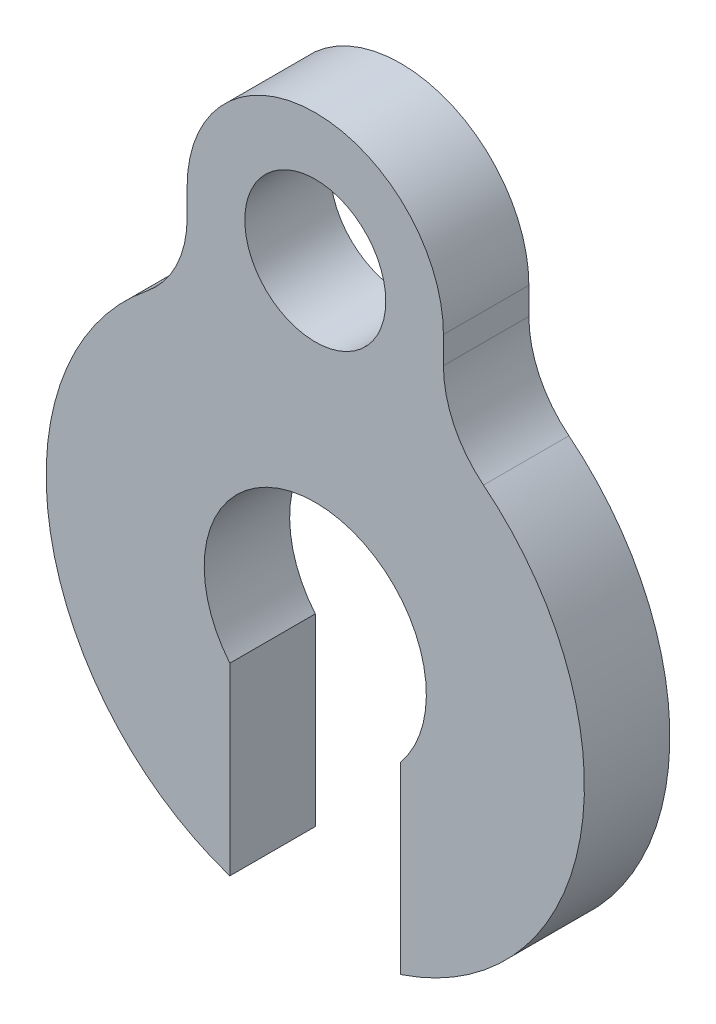
SolidWorks part; units mm, degrees
ref_plane "Front Plane" through (0, 0, 0) normal (0, 0, 1) x (1, 0, 0)
ref_plane "Top Plane" through (0, 0, 0) normal (0, 1, 0) x (1, 0, 0)
ref_plane "Right Plane" through (0, 0, 0) normal (1, 0, 0) x (0, 0, -1)
sketch "Sketch1" plane through (0, 0, 0) normal (0, 0, 1) x (1, 0, 0)
  line L0 (0, -57.8923) -> (0, 2836.7216) construction
  line L1 (-1.905, 3.5178) -> (-1.905, 4.7625)
  line L2 (1.905, 4.7625) -> (1.905, 3.5178)
  line L3 (-1.27, -3.7936) -> (-1.27, -1.0549)
  line L4 (1.27, -3.7936) -> (1.27, -1.0549)
  circle A0 centre (0, 0) radius 1.651 construction
  circle A1 centre (0, 4.7625) radius 1.0478
  arc A2 (-1.905, 4.7625) -> (1.905, 4.7625) centre (0, 4.7625) cw
  arc A3 (-1.905, 3.5178) -> (-1.27, -3.7936) centre (0, 0) ccw
  arc A4 (1.905, 3.5178) -> (1.27, -3.7936) centre (0, 0) cw
  arc A5 (-1.27, -1.0549) -> (1.27, -1.0549) centre (0, 0) cw
  dimension "D1" = 3.302
  dimension "D2" = 2.0955
  dimension "D4" = 1.905
  dimension "D5" = 2.54
  dimension "D6" = 4.0005
  dimension "D3" = 4.7625
extrude "Boss-Extrude1" add sketch "Sketch1" along normal mid plane 1.27 contours L3 A5 L4 A4 L2 A2 L1 A3 A1
fillet "Fillet1" radius 1.5875 2 edges at (-1.905, 3.5178, 0) (1.905, 3.5178, 0)
